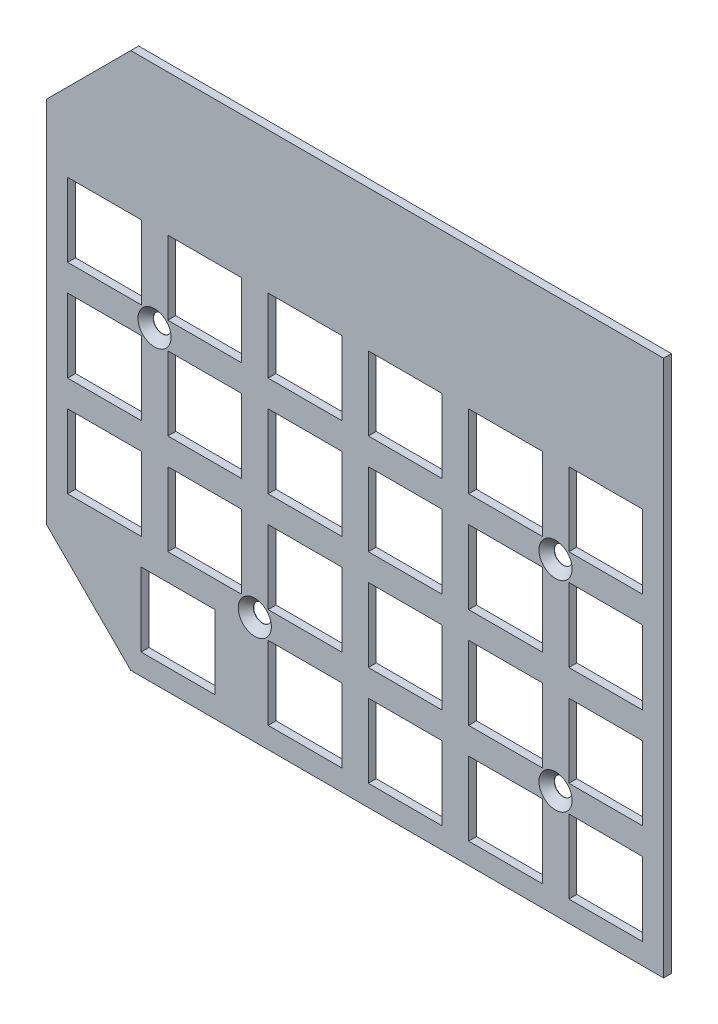
SolidWorks part; units mm, degrees
material "Alliage 1060"
ref_plane "Plan de face" through (0, 0, 0) normal (0, 0, 1) x (1, 0, 0)
ref_plane "Plan de dessus" through (0, 0, 0) normal (0, 1, 0) x (1, 0, 0)
ref_plane "Plan de droite" through (0, 0, 0) normal (1, 0, 0) x (0, 0, -1)
other "Centre de masse"
sketch "Esquisse1" plane through (0, 0, 0) normal (0, 0, 1) x (1, 0, 0)
  line L0 (0, -85) -> (16, -101)
  line L4 (117.25, 1) -> (117.25, -101)
  line L5 (16, 1) -> (0, -15)
  line L7 (117.25, 1) -> (16, 1)
  line L8 (0, -15) -> (0, -85)
  line L9 (16, -101) -> (117.25, -101)
  dimension "D1" = 102
  dimension "D2" = 117.25
  dimension "D3" = 16
  dimension "D4" = 16
  dimension "D5" = 16
  dimension "D6" = 16
extrude "Boss.-Extru.1" add sketch "Esquisse1" along normal blind 1.5
sketch "Esquisse2" plane through (0, 0, 1.5) normal (0, 0, 1) x (1, 0, 0)
  line L1 (4, -25.85) -> (18, -25.85)
  line L2 (4, -25.85) -> (4, -39.85)
  line L3 (4, -39.85) -> (18, -39.85)
  line L4 (18, -25.85) -> (18, -39.85)
  line L5 (11, -39.85) -> (11, -25.85) construction
  line L6 (4, -32.85) -> (18, -32.85) construction
  line L8 (117.25, -101) -> (117.25, 1) construction
  line L12 (23.05, -25.85) -> (23.05, -39.85)
  line L13 (23.05, -25.85) -> (37.05, -25.85)
  line L14 (37.05, -25.85) -> (37.05, -39.85)
  line L15 (23.05, -39.85) -> (37.05, -39.85)
  line L16 (42.1, -25.85) -> (42.1, -39.85)
  line L17 (42.1, -25.85) -> (56.1, -25.85)
  line L18 (56.1, -25.85) -> (56.1, -39.85)
  line L19 (42.1, -39.85) -> (56.1, -39.85)
  line L20 (61.15, -25.85) -> (61.15, -39.85)
  line L21 (61.15, -25.85) -> (75.15, -25.85)
  line L22 (75.15, -25.85) -> (75.15, -39.85)
  line L23 (61.15, -39.85) -> (75.15, -39.85)
  line L24 (80.2, -25.85) -> (80.2, -39.85)
  line L25 (80.2, -25.85) -> (94.2, -25.85)
  line L26 (94.2, -25.85) -> (94.2, -39.85)
  line L27 (80.2, -39.85) -> (94.2, -39.85)
  line L28 (99.25, -25.85) -> (99.25, -39.85)
  line L29 (99.25, -25.85) -> (113.25, -25.85)
  line L30 (113.25, -25.85) -> (113.25, -39.85)
  line L31 (99.25, -39.85) -> (113.25, -39.85)
  line L32 (23.05, -44.9) -> (23.05, -58.9)
  line L33 (23.05, -44.9) -> (37.05, -44.9)
  line L34 (37.05, -44.9) -> (37.05, -58.9)
  line L35 (23.05, -58.9) -> (37.05, -58.9)
  line L36 (42.1, -44.9) -> (42.1, -58.9)
  line L37 (42.1, -44.9) -> (56.1, -44.9)
  line L38 (56.1, -44.9) -> (56.1, -58.9)
  line L39 (42.1, -58.9) -> (56.1, -58.9)
  line L40 (61.15, -44.9) -> (61.15, -58.9)
  line L41 (61.15, -44.9) -> (75.15, -44.9)
  line L42 (75.15, -44.9) -> (75.15, -58.9)
  line L43 (61.15, -58.9) -> (75.15, -58.9)
  line L44 (80.2, -44.9) -> (80.2, -58.9)
  line L45 (80.2, -44.9) -> (94.2, -44.9)
  line L46 (94.2, -44.9) -> (94.2, -58.9)
  line L47 (80.2, -58.9) -> (94.2, -58.9)
  line L48 (99.25, -44.9) -> (99.25, -58.9)
  line L49 (99.25, -44.9) -> (113.25, -44.9)
  line L50 (113.25, -44.9) -> (113.25, -58.9)
  line L51 (99.25, -58.9) -> (113.25, -58.9)
  line L52 (23.05, -63.95) -> (23.05, -77.95)
  line L53 (23.05, -63.95) -> (37.05, -63.95)
  line L54 (37.05, -63.95) -> (37.05, -77.95)
  line L55 (23.05, -77.95) -> (37.05, -77.95)
  line L56 (42.1, -63.95) -> (42.1, -77.95)
  line L57 (42.1, -63.95) -> (56.1, -63.95)
  line L58 (56.1, -63.95) -> (56.1, -77.95)
  line L59 (42.1, -77.95) -> (56.1, -77.95)
  line L60 (61.15, -63.95) -> (61.15, -77.95)
  line L61 (61.15, -63.95) -> (75.15, -63.95)
  line L62 (75.15, -63.95) -> (75.15, -77.95)
  line L63 (61.15, -77.95) -> (75.15, -77.95)
  line L64 (80.2, -63.95) -> (80.2, -77.95)
  line L65 (80.2, -63.95) -> (94.2, -63.95)
  line L66 (94.2, -63.95) -> (94.2, -77.95)
  line L67 (80.2, -77.95) -> (94.2, -77.95)
  line L68 (99.25, -63.95) -> (99.25, -77.95)
  line L69 (99.25, -63.95) -> (113.25, -63.95)
  line L70 (113.25, -63.95) -> (113.25, -77.95)
  line L71 (99.25, -77.95) -> (113.25, -77.95)
  line L72 (4, -44.9) -> (4, -58.9)
  line L73 (4, -44.9) -> (18, -44.9)
  line L74 (18, -44.9) -> (18, -58.9)
  line L75 (4, -58.9) -> (18, -58.9)
  line L76 (4, -63.95) -> (4, -77.95)
  line L77 (4, -63.95) -> (18, -63.95)
  line L78 (18, -63.95) -> (18, -77.95)
  line L79 (4, -77.95) -> (18, -77.95)
  line L112 (42.1, -83) -> (42.1, -97)
  line L113 (42.1, -83) -> (56.1, -83)
  line L114 (56.1, -83) -> (56.1, -97)
  line L115 (42.1, -97) -> (56.1, -97)
  line L116 (61.15, -83) -> (61.15, -97)
  line L117 (61.15, -83) -> (75.15, -83)
  line L118 (75.15, -83) -> (75.15, -97)
  line L119 (61.15, -97) -> (75.15, -97)
  line L120 (80.2, -83) -> (80.2, -97)
  line L121 (80.2, -83) -> (94.2, -83)
  line L122 (94.2, -83) -> (94.2, -97)
  line L123 (80.2, -97) -> (94.2, -97)
  line L124 (99.25, -83) -> (99.25, -97)
  line L125 (99.25, -83) -> (113.25, -83)
  line L126 (113.25, -83) -> (113.25, -97)
  line L127 (99.25, -97) -> (113.25, -97)
  line L128 (4, -83) -> (4, -97) [skipped]
  line L129 (4, -83) -> (18, -83) [skipped]
  line L130 (18, -83) -> (18, -97) [skipped]
  line L131 (4, -97) -> (18, -97) [skipped]
  line L132 (23.05, -83) -> (23.05, -97) [skipped]
  line L133 (23.05, -83) -> (37.05, -83) [skipped]
  line L134 (37.05, -83) -> (37.05, -97) [skipped]
  line L135 (23.05, -97) -> (37.05, -97) [skipped]
  line L137 (17.97, -83) -> (31.97, -83)
  line L138 (17.97, -83) -> (17.97, -97)
  line L139 (17.97, -97) -> (31.97, -97)
  line L140 (31.97, -83) -> (31.97, -97)
  line L141 (24.97, -97) -> (24.97, -83) construction
  line L142 (17.97, -90) -> (31.97, -90) construction
  line L143 (16, -101) -> (117.25, -101) construction
  point P0 (11, -32.85)
  point P19 (24.97, -90)
  dimension "D5" = 4
  dimension "D13" = 5.05
  dimension "D1" = 14
  dimension "D2" = 14
  dimension "D3" = 4
  dimension "D4" = 6
  dimension "D9" = 14
  dimension "D10" = 14
  dimension "D11" = 10.13
  dimension "D12" = 5.05
  dimension "D8" = 4
extrude "Enlèv. mat.-Extru.1" cut sketch "Esquisse2" against normal blind 1.5
sketch "Esquisse9" plane through (0, 0, 1.5) normal (0, 0, 1) x (1, 0, 0)
  line L0 (18, -44.9) -> (23.05, -39.85) construction
  line L1 (94.2, -39.85) -> (99.25, -44.9) construction
  line L2 (94.2, -83) -> (99.25, -77.95) construction
  line L3 (37.05, -77.95) -> (42.1, -83) construction
  point P16 (20.525, -42.375)
  point P17 (39.575, -80.475)
  point P18 (96.725, -42.375)
  point P19 (96.725, -80.475)
hole_wizard "Fraisage pour vis à tête fraisée M31" positions "Esquisse17" profile "Esquisse18" countersink size "M3" standard "Ansi Metric" end condition through all
sketch "Esquisse17" plane through (0, 0, 1.5) normal (0, 0, 1) x (1, 0, 0)
  point P0 (20.525, -42.375)
  point P4 (96.725, -42.375)
  point P7 (96.725, -80.475)
  point P10 (39.575, -80.475)
sketch "Esquisse18" plane through (20.525, -42.375, 1.5) normal (1, 0, 0) x (0, -1, 0)
  line L0 (0, 0) -> (0, 1.5)
  line L1 (0, 1.5) -> (1.7, 1.5)
  line L2 (1.7, 1.5) -> (1.7, 1.45)
  line L3 (1.7, 1.45) -> (3.15, 0)
  line L5 (3.15, 0) -> (0, 0)
  line L6 (-1.7, 1.45) -> (-3.15, 0) construction
  line L11 (0, -6.35) -> (0, 107.95) construction
  dimension "Diamètre du perçage jusqu'au prochain" = 3.4
  dimension "Profondeur du perçage jusqu'au prochain" = 1.5
  dimension "Diamètre du fraisage entrant" = 6.3
  dimension "Angle du fraisage entrant" = 90
